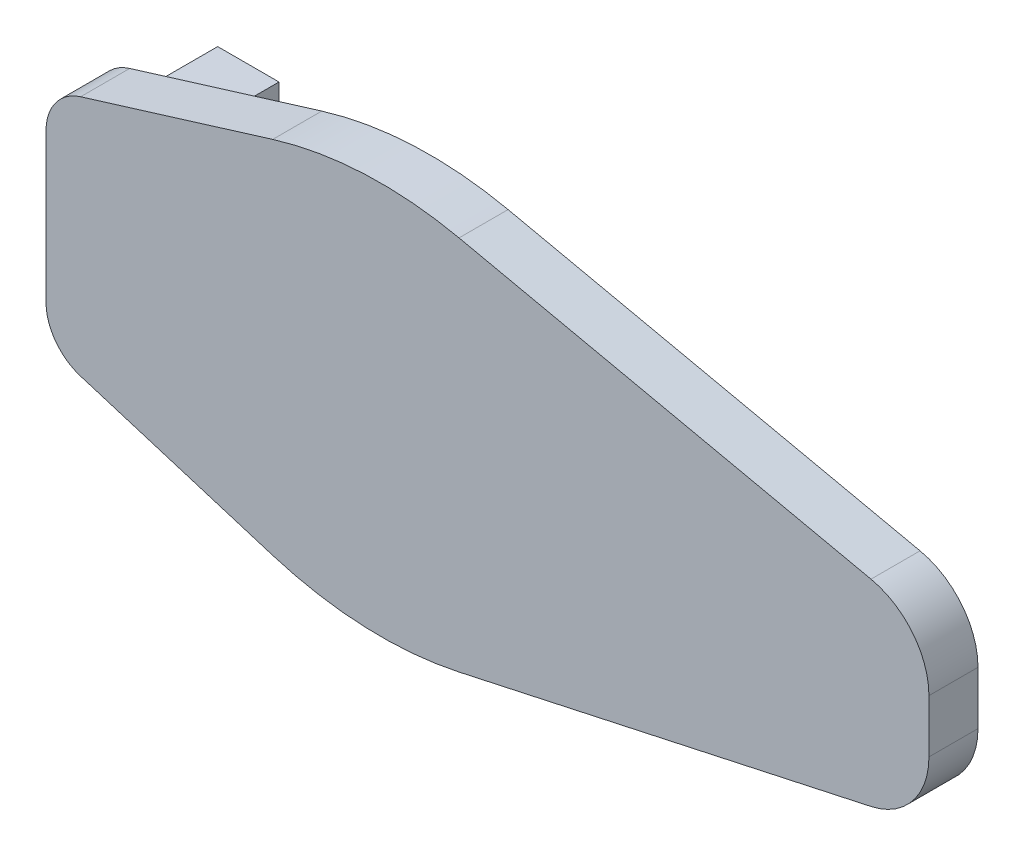
SolidWorks part; units mm, degrees
ref_plane "Front" through (0, 0, 0) normal (0, 0, 1) x (1, 0, 0)
ref_plane "Top" through (0, 0, 0) normal (0, 1, 0) x (1, 0, 0)
ref_plane "Right" through (0, 0, 0) normal (1, 0, 0) x (0, 0, -1)
sketch "Sketch1" plane through (0, 0, 0) normal (0, 0, 1) x (1, 0, 0)
  line L0 (2.8237, 9.8688) -> (18.4864, 14.6881)
  line L1 (33.6818, 15.33) -> (67.2746, 8.0273)
  line L2 (72, 2.1642) -> (72, -2.1642)
  line L3 (0, 6.0457) -> (0, -6.0457)
  line L4 (0, 0) -> (72, 0) construction
  line L5 (33.6818, -15.33) -> (67.2746, -8.0273)
  line L6 (2.8237, -9.8688) -> (18.4864, -14.6881)
  arc A0 (33.6818, 15.33) -> (18.4864, 14.6881) centre (27.3089, -13.9853) ccw
  arc A1 (67.2746, 8.0273) -> (72, 2.1642) centre (66, 2.1642) cw
  arc A2 (2.8237, 9.8688) -> (0, 6.0457) centre (4, 6.0457) ccw
  arc A3 (2.8237, -9.8688) -> (0, -6.0457) centre (4, -6.0457) cw
  arc A4 (67.2746, -8.0273) -> (72, -2.1642) centre (66, -2.1642) ccw
  arc A5 (33.6818, -15.33) -> (18.4864, -14.6881) centre (27.3089, 13.9853) cw
  point P8 (26, 17)
  point P11 (72, 7)
  point P14 (0, 9)
  dimension "D6" = 30
  dimension "D7" = 6
  dimension "D8" = 4
  dimension "D1" = 17
  dimension "D2" = 72
  dimension "D3" = 26
  dimension "D4" = 7
  dimension "D5" = 9
extrude "Boss-Extrude1" add sketch "Sketch1" along normal blind 4
sketch "Sketch2" plane through (0, 0, 0) normal (0, 0, -1) x (-1, 0, 0)
  line L1 (-5, -5) -> (0, -5)
  line L2 (-5, -5) -> (-5, 5)
  line L3 (-5, 5) -> (0, 5)
  line L4 (0, -5) -> (0, 5)
  line L5 (-5, -5) -> (0, 5) construction
  line L6 (-5, 5) -> (0, -5) construction
  point P0 (-2.5, 0)
  dimension "D1" = 10
  dimension "D2" = 5
  dimension "D3" = 0
extrude "Boss-Extrude2" add sketch "Sketch2" along normal blind 10
sketch "Sketch3" plane through (5, 0, 0) normal (1, 0, 0) x (0, 0, -1)
  line L0 (0, -5) -> (10, 5) construction
  circle A0 centre (5, 0) radius 1.55
  dimension "D1" = 3.1
extrude "Cut-Extrude1" cut sketch "Sketch3" against normal up to next
